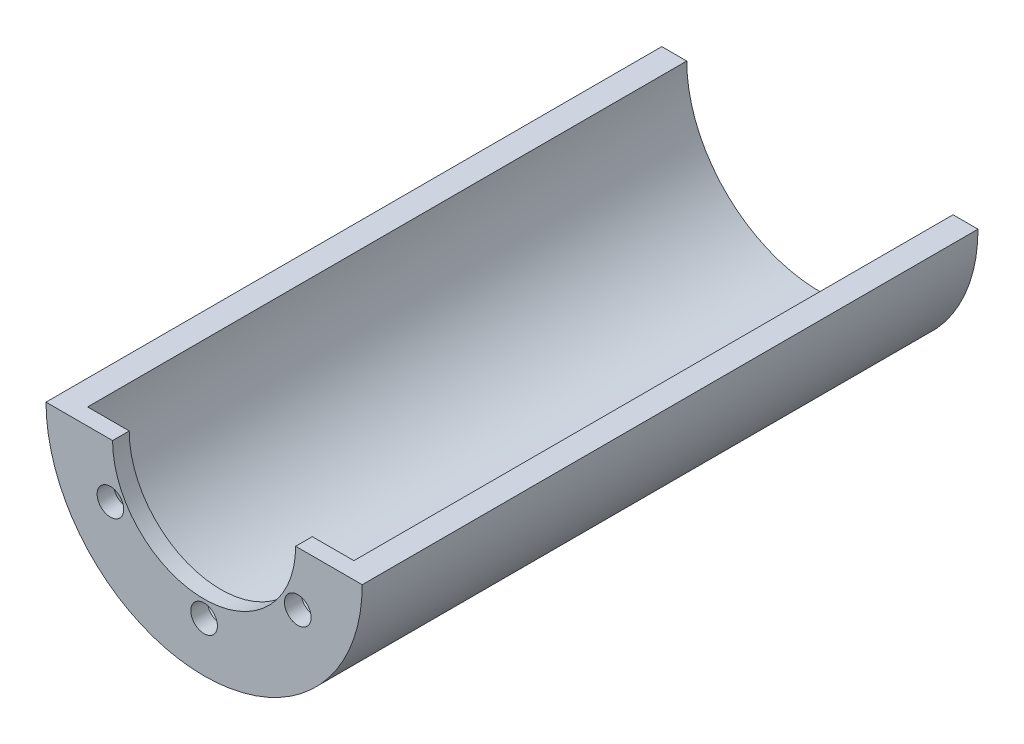
SolidWorks part; units mm, degrees
material "Ti-6Al-4VSolution treated and aged (SS)"
ref_plane "Front Plane" through (0, 0, 0) normal (0, 0, 1) x (1, 0, 0)
ref_plane "Top Plane" through (0, 0, 0) normal (0, 1, 0) x (1, 0, 0)
ref_plane "Right Plane" through (0, 0, 0) normal (1, 0, 0) x (0, 0, -1)
sketch "Sketch1" plane through (0, 0, 0) normal (0, 0, 1) x (1, 0, 0)
  circle A0 centre (0, 0) radius 9.5
  dimension "D1" = 19
extrude "Boss-Extrude1" add sketch "Sketch1" along normal blind 36
sketch "Sketch2" plane through (0, 0, 36) normal (0, 0, 1) x (1, 0, 0)
  circle A0 centre (0, 0) radius 8
  dimension "D1" = 16
extrude "Cut-Extrude1" cut sketch "Sketch2" against normal through all
sketch "Sketch4" plane through (0, 0, 36) normal (0, 0, 1) x (1, 0, 0)
  line L0 (-11.688, 0) -> (14.7909, 0) construction
  line L1 (-9.5, 0) -> (9.5, 0)
  line L2 (-9.5, 0) -> (-9.5, 9.5)
  line L3 (-9.5, 9.5) -> (9.5, 9.5)
  line L4 (9.5, 0) -> (9.5, 9.5)
  line L5 (9.5, 0) -> (9.5, 6.2077) construction
  line L6 (-9.5, 0) -> (-9.5, 0.9729) construction
  line L7 (0, 9.5) -> (7.7472, 9.5) construction
  circle A0 centre (0, 0) radius 9.5 construction
extrude "Cut-Extrude2" cut sketch "Sketch4" against normal through all
sketch "Sketch5" plane through (0, 0, 36) normal (0, 0, 1) x (1, 0, 0)
  line L0 (-9.5, 0) -> (9.5, 0)
  arc A0 (9.5, 0) -> (0, -9.5) centre (0, 0) cw
  arc A1 (-9.5, 0) -> (9.5, 0) centre (0, 0) ccw construction
  arc A2 (-9.5, 0) -> (9.5, 0) centre (0, 0) ccw
  line M3 (-8, 0) -> (-9.5, 0)
  arc M4 (-9.5, 0) -> (9.5, 0) centre (0, 0) ccw
  line M5 (9.5, 0) -> (8, 0)
  arc M6 (8, 0) -> (-8, 0) centre (0, 0) cw
extrude "Boss-Extrude3" add sketch "Sketch5" along normal blind 1 contours M6 M3 M4 M5 | L0 M6
sketch "Sketch8" plane through (0, 0, 37) normal (0, 0, 1) x (1, 0, 0)
  line L0 (9.5, 0) -> (-9.5, 0) construction
  circle A0 centre (0, 0) radius 5.5
  dimension "D1" = 11
extrude "Cut-Extrude9" cut sketch "Sketch8" against normal through all
sketch "Sketch9" plane through (0, 0, 36) normal (0, 0, -1) x (-1, 0, 0)
  line L0 (0, -5.5) -> (0, -7.5) construction
  arc A0 (-5.5, 0) -> (5.5, 0) centre (0, 0) ccw construction
  circle A1 centre (0, -6.5) radius 0.8
  arc A3 (-8, 0) -> (8, 0) centre (0, 0) ccw construction
  circle A4 centre (0, 0) radius 6.5 construction
  point P12 (0, -8)
  dimension "D1" = 1.6
  dimension "D2" = 1.5
extrude "Cut-Extrude10" cut sketch "Sketch9" against normal through all
pattern_circular "CirPattern2" count 6 over 360 about axis through (0, 0, 0) along (0, 0, 1) of "Cut-Extrude10"
